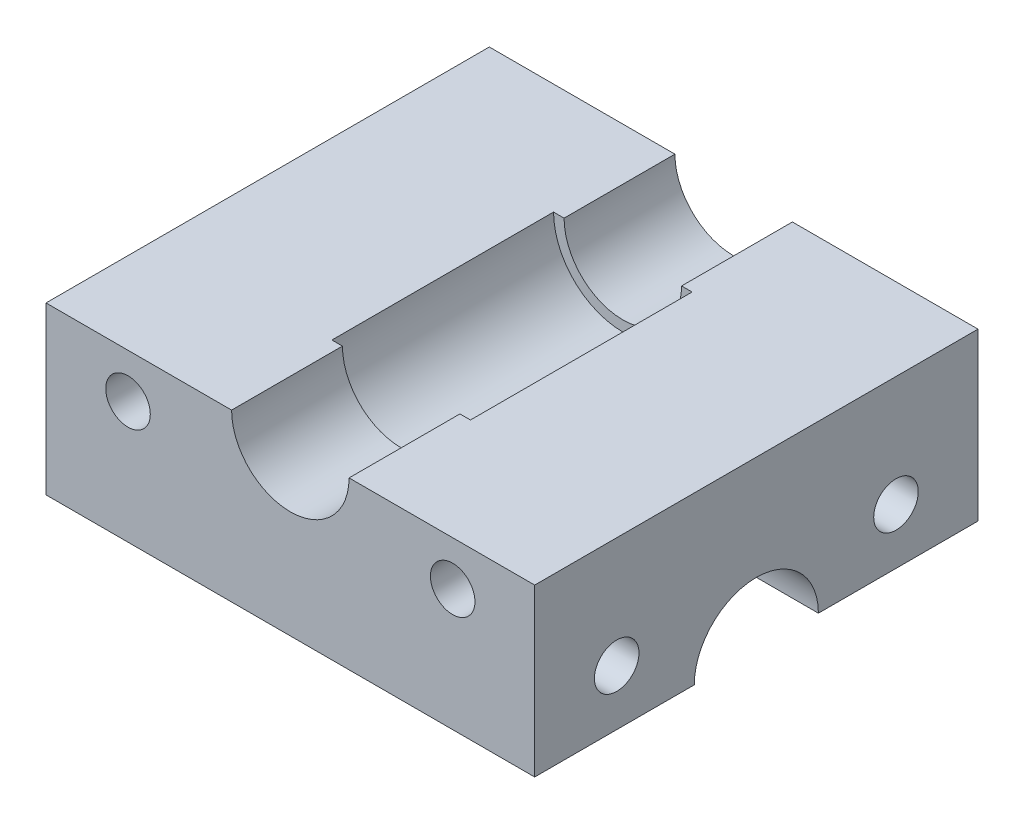
SolidWorks part; units mm, degrees
material "ABS"
ref_plane "Front Plane" through (0, 0, 0) normal (0, 0, 1) x (1, 0, 0)
ref_plane "Top Plane" through (0, 0, 0) normal (0, 1, 0) x (1, 0, 0)
ref_plane "Right Plane" through (0, 0, 0) normal (1, 0, 0) x (0, 0, -1)
sketch "Sketch1" plane through (0, 0, 0) normal (0, 0, 1) x (1, 0, 0)
  line L0 (23.737, 16.5733) -> (45.006, 16.5733)
  line L1 (-10.994, -2.4767) -> (45.006, -2.4767)
  line L2 (-10.994, -2.4767) -> (-10.994, 16.5733)
  line L3 (-10.994, 16.5733) -> (10.275, 16.5733)
  line L4 (45.006, -2.4767) -> (45.006, 16.5733)
  line L5 (17.006, -2.4767) -> (17.006, 54.6755) construction
  arc A0 (23.737, 16.5733) -> (10.275, 16.5733) centre (17.006, 16.5733) cw
  dimension "D3" = 6.731
  dimension "D1" = 19.05
  dimension "D2" = 56
extrude "Boss-Extrude1" add sketch "Sketch1" along normal blind 50.8
ref_plane "Plane1" through (0, 0, 25.4) normal (0, 0, 1) x (1, 0, 0)
sketch "Sketch2" plane through (0, 0, 25.4) normal (0, 0, 1) x (1, 0, 0)
  circle A0 centre (17.006, 16.5733) radius 7.9375
  dimension "D1" = 15.875
extrude "Cut-Extrude1" cut sketch "Sketch2" against normal mid plane 25.4
hole_wizard "#10 Clearance Hole1" positions "3DSketch1" profile "Sketch5" hole size "#10" standard "ANSI Inch" end condition through all
sketch3d "3DSketch1"
  line L0 (-10.994, -2.4767, 50.8) -> (-10.994, -2.4767, 0) construction
  line L1 (-10.994, 16.5733, 50.8) -> (-10.994, -2.4767, 50.8) construction
  line L2 (-10.994, 16.5733, 0) -> (-10.994, -2.4767, 0) construction
  line L3 (45.006, -2.4767, 50.8) -> (45.006, 16.5733, 50.8) construction
  line L4 (-10.994, -2.4767, 50.8) -> (45.006, -2.4767, 50.8) construction
  point P0 (-10.994, 3.8733, 41.402)
  point P4 (-1.596, 11.4933, 50.8)
  point P6 (35.608, 11.4933, 50.8)
  point P20 (-10.994, 3.8733, 9.398)
  dimension "D1" = 6.35
  dimension "D2" = 9.398
  dimension "D3" = 9.398
  dimension "D4" = 9.398
  dimension "D5" = 9.398
  dimension "D6" = 13.97
sketch "Sketch5" plane through (-10.994, 3.8733, 41.402) normal (0, 1, 0) x (0, 0, 1)
  line L0 (0, 0) -> (0, 56)
  line L1 (0, 56) -> (2.5527, 56)
  line L2 (2.5527, 56) -> (2.5527, 0)
  line L5 (2.5527, 0) -> (0, 0)
  line L11 (0, -6.35) -> (0, 107.95) construction
  dimension "Thru Hole Dia." = 5.1054
  dimension "Thru Hole Depth" = 56
sketch "Sketch9" plane through (45.006, 0, 0) normal (1, 0, 0) x (0, 0, -1)
  line L0 (-50.8, -2.4767) -> (0, -2.4767) construction
  line L1 (-32.512, -2.4767) -> (-18.288, -2.4767)
  arc A0 (-18.288, -2.4767) -> (-32.512, -2.4767) centre (-25.4, -2.4767) ccw
  circle A1 centre (-9.398, 3.8733) radius 2.5527 construction
  dimension "D1" = 8.89
extrude "Cut-Extrude4" cut sketch "Sketch9" against normal through all contours A0 L1
equation "\"D2@3DSketch1\"=\"D3@3DSketch1\""
equation "\"D4@3DSketch1\"=\"D3@3DSketch1\""
equation "\"D5@3DSketch1\"=\"D3@3DSketch1\""
